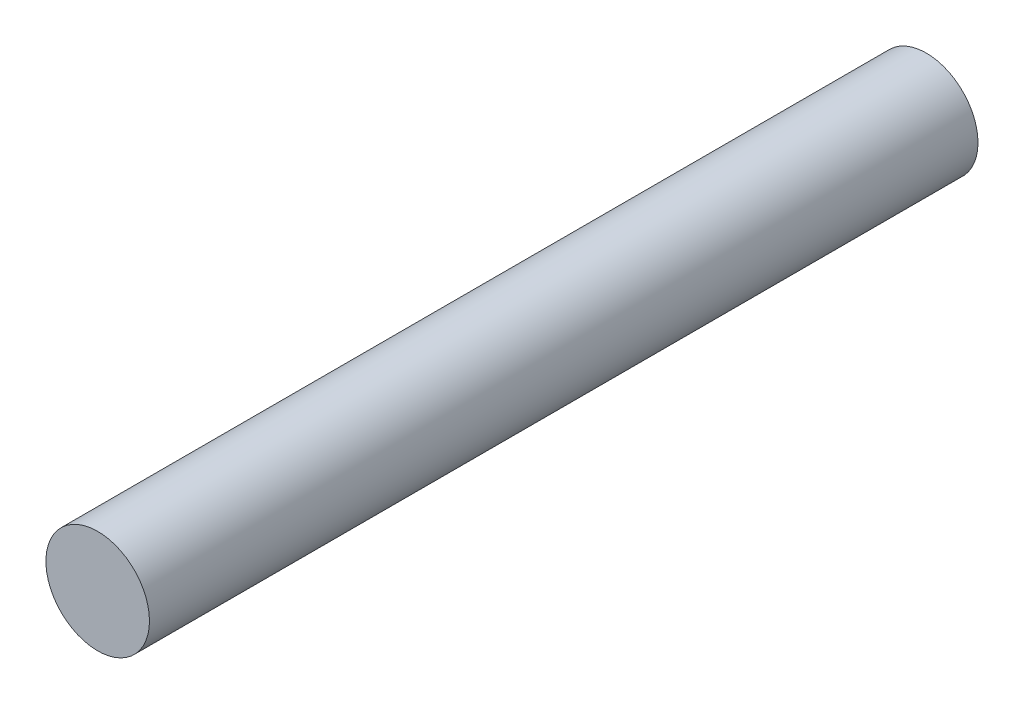
SolidWorks part; units mm, degrees
ref_plane "Front Plane" through (0, 0, 0) normal (0, 0, 1) x (1, 0, 0)
ref_plane "Top Plane" through (0, 0, 0) normal (0, 1, 0) x (1, 0, 0)
ref_plane "Right Plane" through (0, 0, 0) normal (1, 0, 0) x (0, 0, -1)
ref_plane "Plane4"
sketch "Sketch1" plane through (0, 0, 0) normal (0, 0, 1) x (1, 0, 0)
  circle A0 centre (0, 0) radius 3.175
  dimension "D1" = 6.35
extrude "Extrusion1" add sketch "Sketch1" along normal blind 50.8
